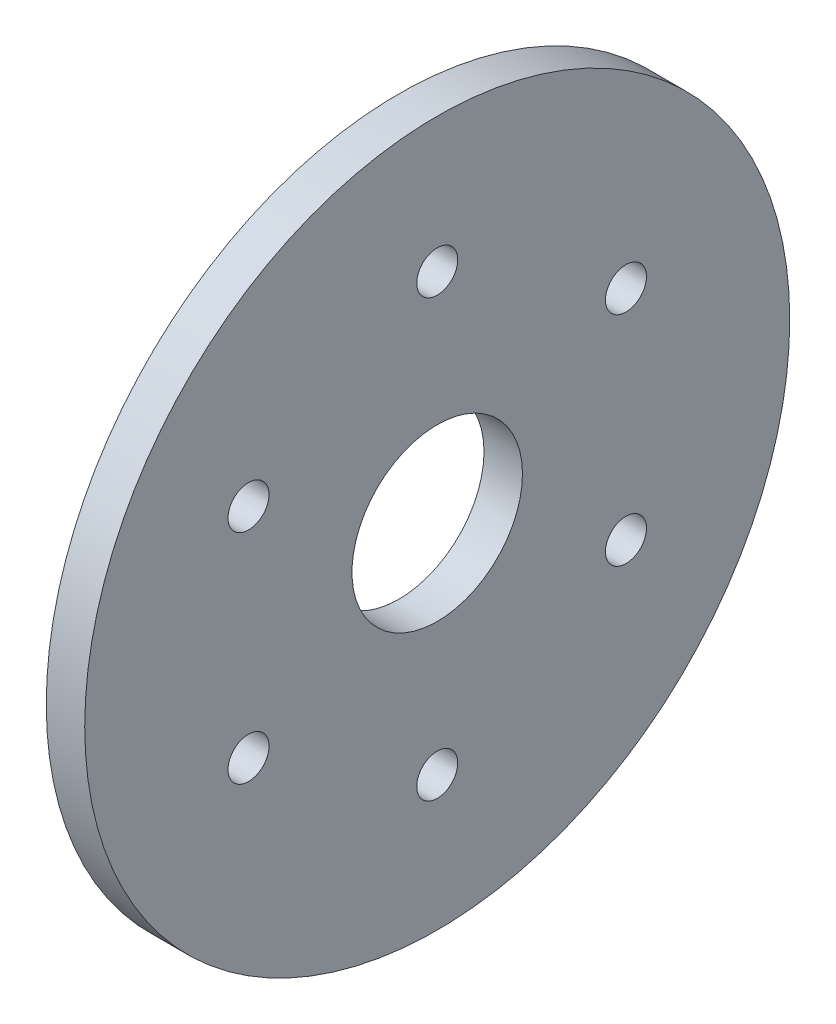
SolidWorks part; units mm, degrees
ref_plane "Front Plane" through (0, 0, 0) normal (0, 0, 1) x (1, 0, 0)
ref_plane "Top Plane" through (0, 0, 0) normal (0, 1, 0) x (1, 0, 0)
ref_plane "Right Plane" through (0, 0, 0) normal (1, 0, 0) x (0, 0, -1)
sketch "Sketch1" plane through (0, 0, 0) normal (1, 0, 0) x (0, 0, -1)
  circle A0 centre (0, 0) radius 27.5
  circle A1 centre (0, 0) radius 6.65
  dimension "D1" = 55
  dimension "D2" = 13.3
extrude "Boss-Extrude1" add sketch "Sketch1" along normal blind 3
sketch "Sketch3" plane through (3, 0, 0) normal (1, 0, 0) x (0, 0, -1)
  line L0 (0, 0) -> (0, 27.5) construction
  circle A0 centre (0, 0) radius 27.5 construction
  circle A1 centre (0, 17) radius 1.6
  circle A2 centre (14.7224, 8.5) radius 1.6
  circle A3 centre (14.7224, -8.5) radius 1.6
  circle A4 centre (0, -17) radius 1.6
  circle A5 centre (-14.7224, -8.5) radius 1.6
  circle A6 centre (-14.7224, 8.5) radius 1.6
  point P20 (0, 0)
  dimension "D1" = 3.2
  dimension "D2" = 17
  dimension "D3" = 6
extrude "Cut-Extrude1" cut sketch "Sketch3" against normal through all
